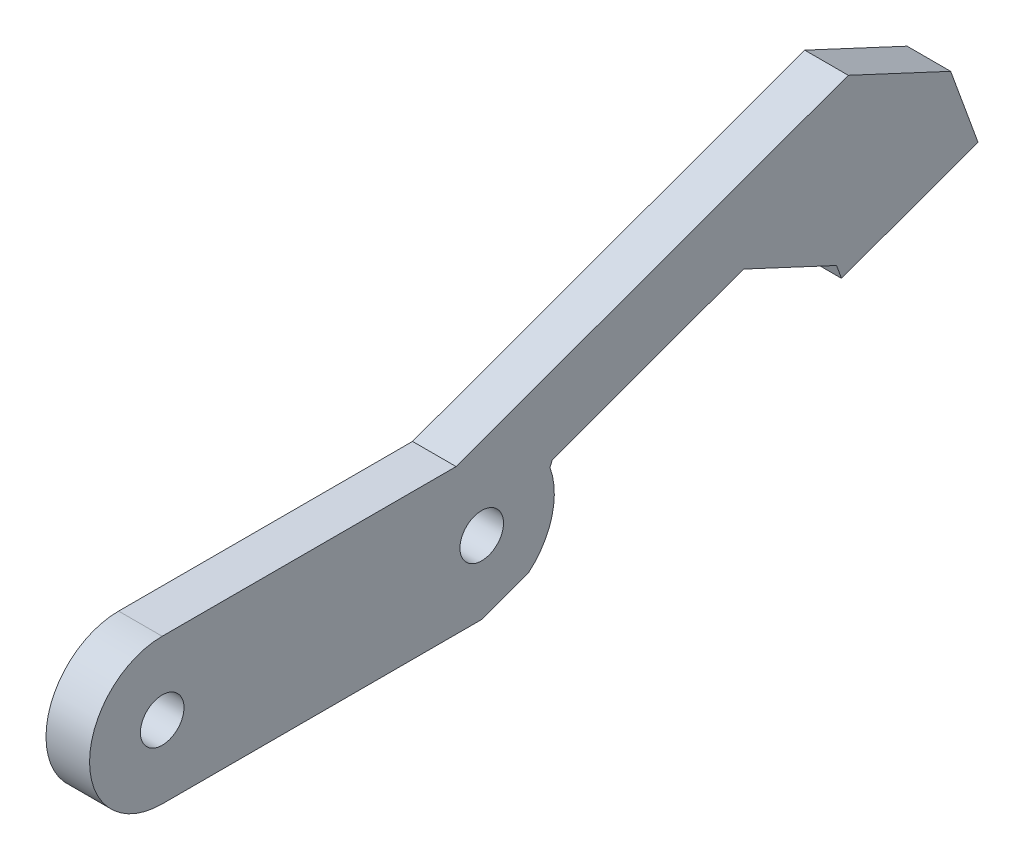
SolidWorks part; units mm, degrees
ref_plane "Front Plane" through (0, 0, 0) normal (0, 0, 1) x (1, 0, 0)
ref_plane "Top Plane" through (0, 0, 0) normal (0, 1, 0) x (1, 0, 0)
ref_plane "Right Plane" through (0, 0, 0) normal (1, 0, 0) x (0, 0, -1)
sketch "Sketch1" plane through (0, 0, 0) normal (1, 0, 0) x (0, 0, -1)
  line L1 (0, 0) -> (27, 0)
  line L2 (0, 0) -> (0, 10)
  line L3 (0, 10) -> (27, 10)
  circle A0 centre (5, 5) radius 1.5
  circle A1 centre (5, 5) radius 5
  circle A2 centre (27, 5) radius 5
  circle A3 centre (27, 5) radius 1.5
  dimension "D7" = 3
  dimension "D11" = 10
  dimension "D2" = 3
  dimension "D1" = 10
  dimension "D8" = 5
  dimension "D9" = 5
  dimension "D10" = 22
extrude "Boss-Extrude1" add sketch "Sketch1" along normal blind 3 contours A1 A0 | A2 L3 A1 L1 | A2 A3
sketch "Sketch2" plane through (3, 0, 0) normal (1, 0, 0) x (0, 0, -1)
  line L0 (27, 0) -> (60.8289, 12.3127)
  line L1 (5, 0) -> (27, 0) construction
  line L3 (60.8289, 12.3127) -> (57.4087, 21.7097)
  line L5 (57.4087, 21.7097) -> (25.2367, 10)
  line L6 (5, 10) -> (27, 10) construction
  line L7 (31.8677, 7.0926) -> (45.0234, 11.8809)
  line L8 (31.8677, 7.0926) -> (28.8794, 0.684)
  line L9 (45.0234, 11.8809) -> (51.432, 8.8925)
  line L10 (51.432, 8.8925) -> (60.8289, 12.3127)
  line L11 (51.432, 8.8925) -> (51.774, 7.9528)
  line L12 (60.8289, 12.3127) -> (61.171, 11.373)
  line L13 (51.774, 7.9528) -> (61.171, 11.373)
  line L14 (5, 10) -> (27, 10)
  arc A0 (5, 10) -> (5, 0) centre (5, 5) ccw construction
  arc A2 (5, 10) -> (5, 0) centre (5, 5) ccw construction
  arc A3 (27, 0) -> (27, 10) centre (27, 5) ccw construction
  arc A4 (27, 0) -> (27, 10) centre (27, 5) ccw
  line M1 (27, 10) -> (5, 10)
  arc M4 (27, 0) -> (27, 10) centre (27, 5) ccw
  dimension "D1" = 160
  dimension "D2" = 36
  dimension "D3" = 90
  dimension "D4" = 10
  dimension "D5" = 10
  dimension "D6" = 45
  dimension "D7" = 45
  dimension "D8" = 5
  dimension "D9" = 5
  dimension "D10" = 14
  dimension "D11" = 1
extrude "Boss-Extrude2" add sketch "Sketch2" against normal blind 3 contours L7 L9 L0 L3 L5 L8 M1 M4 | L11 L13 L12 L0
sketch "Sketch3" plane through (3, 0, 0) normal (1, 0, 0) x (0, 0, -1)
  line L0 (51.432, 8.8925) -> (27, 0)
  line L1 (5, 0) -> (27, 0) construction
  circle A0 centre (27, 5) radius 5
  arc M4 (27, 0) -> (31.6945, 6.721) centre (27, 5) ccw
  dimension "D1" = 160
extrude "Cut-Extrude1" cut sketch "Sketch3" against normal blind 3 contours L0 M4
sketch "Sketch4" plane through (3, 0, 0) normal (1, 0, 0) x (0, 0, -1)
  line L0 (52.2404, 19.8285) -> (59.2898, 16.5413)
  line L1 (57.4087, 21.7097) -> (25.2367, 10) construction
  line L2 (61.171, 11.373) -> (57.4087, 21.7097) construction
  line L3 (45.0234, 11.8809) -> (51.432, 8.8925) construction
  line L4 (57.4087, 21.7097) -> (25.2367, 10)
  line L5 (61.171, 11.373) -> (57.4087, 21.7097)
  line M8 (61.171, 11.373) -> (57.4087, 21.7097)
  line M9 (57.4087, 21.7097) -> (25.2367, 10)
extrude "Cut-Extrude2" cut sketch "Sketch4" against normal through all contours L0 M9 M8
